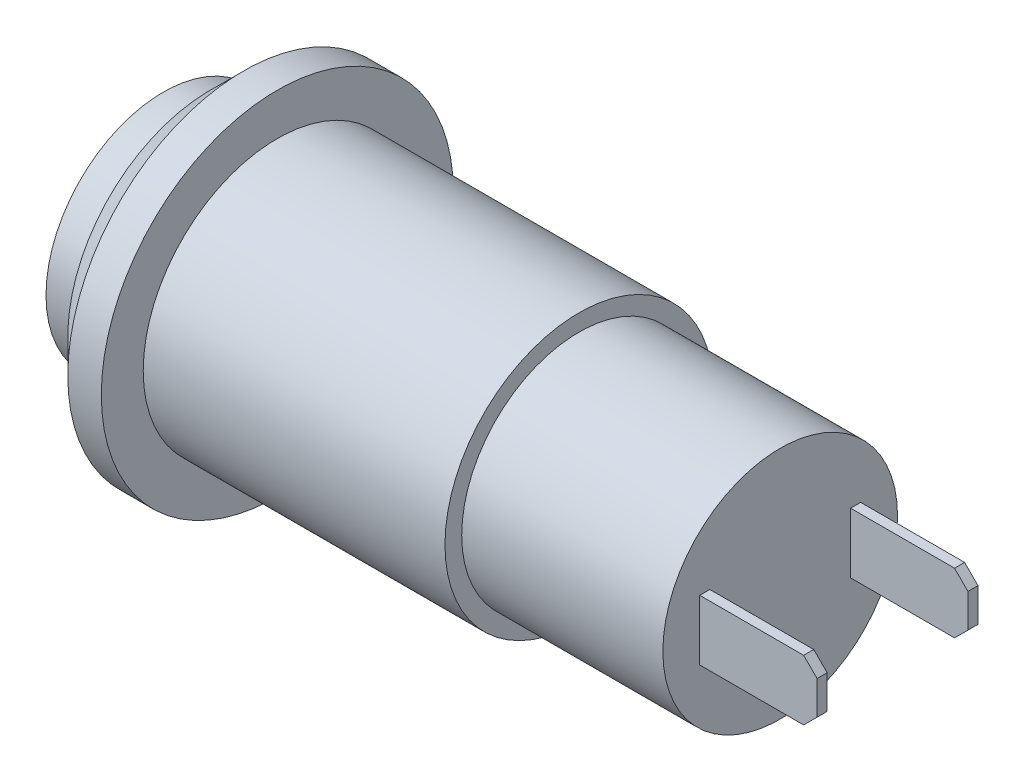
SolidWorks part; units mm, degrees
ref_plane "前视基准面" through (0, 0, 0) normal (0, 0, 1) x (1, 0, 0)
ref_plane "上视基准面" through (0, 0, 0) normal (0, 1, 0) x (1, 0, 0)
ref_plane "右视基准面" through (0, 0, 0) normal (1, 0, 0) x (0, 0, -1)
sketch "草图1" plane through (0, 0, 0) normal (0, 0, 1) x (1, 0, 0)
  line L0 (0, 0) -> (18.4, 0) construction
  line L1 (18.4, 0) -> (18.4, 3.5)
  line L2 (18.4, 3.5) -> (12.4, 3.5)
  line L3 (12.4, 3.5) -> (12.4, 4)
  line L4 (12.4, 4) -> (3.4, 4)
  line L5 (3.4, 4) -> (3.4, 5.25)
  line L6 (3.4, 5.25) -> (1.4, 5.25)
  line L7 (1.4, 5.25) -> (1.4, 3.5)
  line L8 (1.4, 3.5) -> (0, 3.5)
  line L9 (0, 3.5) -> (0, 0)
  line L10 (0, 0) -> (18.4, 0)
  dimension "D1" = 3.5
  dimension "D2" = 3.5
  dimension "D3" = 1.4
  dimension "D4" = 2
  dimension "D5" = 9
  dimension "D6" = 4
  dimension "D7" = 10.5
  dimension "D8" = 18.4
revolve "旋转1" add sketch "草图1" angle 360 about L0
cosmetic thread "装饰螺纹线1" parameters "D2"=7
chamfer "倒角1" distance 1 angle 45 1 edges at (1.4, 0, 5.25)
sketch "草图2" plane through (18.4, 0, 0) normal (1, 0, 0) x (0, 0, -1)
  line L0 (-2.25, 0) -> (2.25, 0) construction
  line L1 (0, -1.7543) -> (0, 1.7543) construction
  line L2 (2.1, 0.9) -> (2.4, 0.9)
  line L3 (2.1, 0.9) -> (2.1, -0.9)
  line L4 (2.1, -0.9) -> (2.4, -0.9)
  line L5 (2.4, 0.9) -> (2.4, -0.9)
  line L6 (2.1, 0.9) -> (2.4, -0.9) construction
  line L7 (2.1, -0.9) -> (2.4, 0.9) construction
  line L12 (-2.4, 0.9) -> (-2.4, -0.9)
  line L13 (-2.1, -0.9) -> (-2.4, -0.9)
  line L14 (-2.1, 0.9) -> (-2.1, -0.9)
  line L15 (-2.1, 0.9) -> (-2.4, 0.9)
  point P4 (0, 0)
  point P15 (0, 0)
  dimension "D1" = 1.8
  dimension "D2" = 0.3
  dimension "D3" = 2.4
extrude "凸台-拉伸1" add sketch "草图2" along normal blind 3.5
chamfer "倒角3" distance 0.4 angle 45 4 edges at (21.9, -0.9, -2.25) (21.9, 0.9, -2.25) (21.9, -0.9, 2.25) (21.9, 0.9, 2.25)
